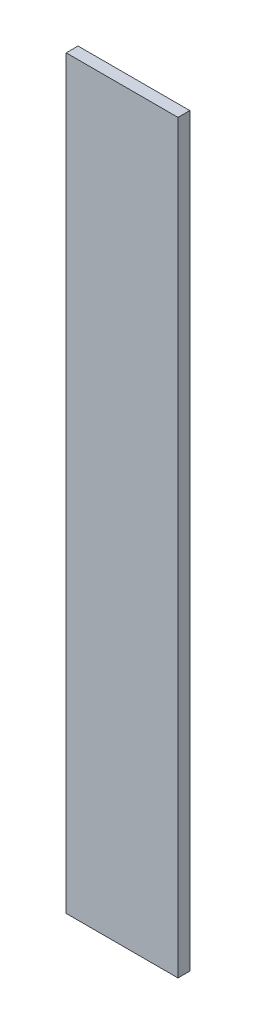
SolidWorks part; units mm, degrees
ref_plane "Front Plane" through (0, 0, 0) normal (0, 0, 1) x (1, 0, 0)
ref_plane "Top Plane" through (0, 0, 0) normal (0, 1, 0) x (1, 0, 0)
ref_plane "Right Plane" through (0, 0, 0) normal (1, 0, 0) x (0, 0, -1)
sketch "Sketch1" plane through (0, 0, 0) normal (0, 0, 1) x (1, 0, 0)
  line L1 (15, -100) -> (-15, -100)
  line L2 (15, -100) -> (15, 100)
  line L3 (15, 100) -> (-15, 100)
  line L4 (-15, -100) -> (-15, 100)
  line L5 (15, -100) -> (-15, 100) construction
  line L6 (15, 100) -> (-15, -100) construction
  point P0 (0, 0)
  dimension "D1" = 30
  dimension "D2" = 200
extrude "Boss-Extrude1" add sketch "Sketch1" along normal blind 3.175
